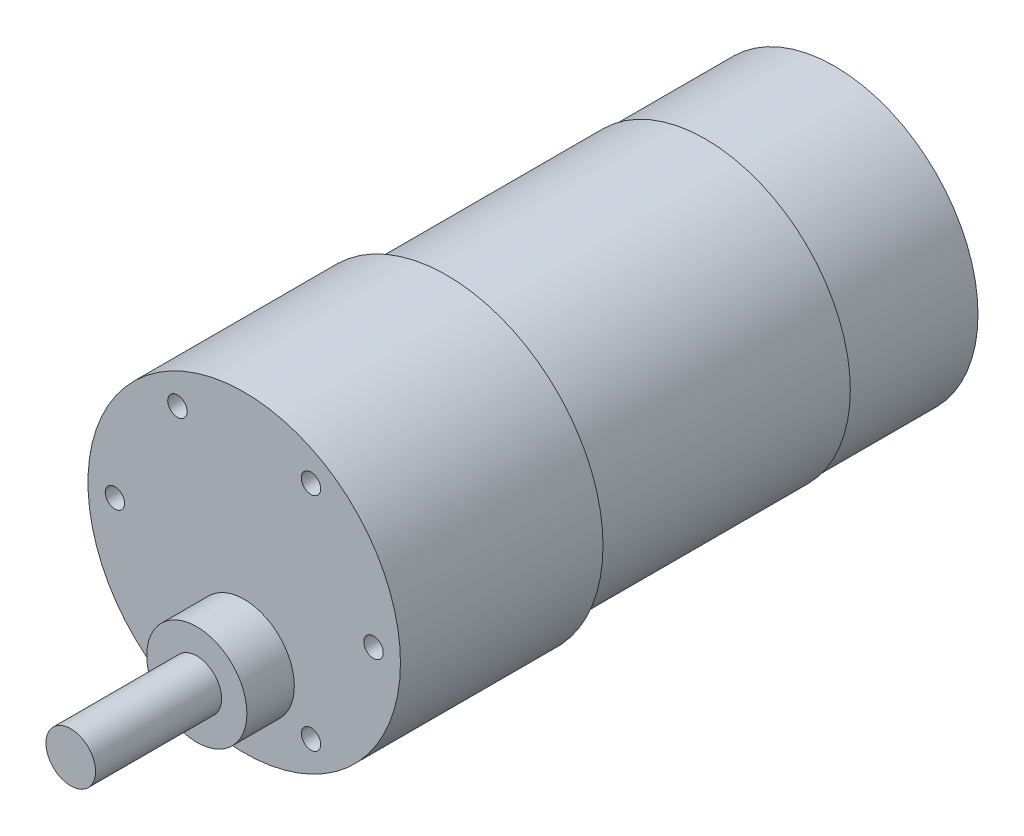
SolidWorks part; units mm, degrees
ref_plane "Front Plane" through (0, 0, 0) normal (0, 0, 1) x (1, 0, 0)
ref_plane "Top Plane" through (0, 0, 0) normal (0, 1, 0) x (1, 0, 0)
ref_plane "Right Plane" through (0, 0, 0) normal (1, 0, 0) x (0, 0, -1)
sketch "Sketch1" plane through (0, 0, 0) normal (0, 0, 1) x (1, 0, 0)
  circle A0 centre (0, 0) radius 18.415
  dimension "D1" = 36.83
extrude "Boss-Extrude1" add sketch "Sketch1" against normal blind 23.876
sketch "Sketch2" plane through (0, 0, 0) normal (0, 0, 1) x (1, 0, 0)
  circle A0 centre (0, -8.636) radius 5.9055
  dimension "D1" = 11.811
  dimension "D2" = 8.636
extrude "Boss-Extrude2" add sketch "Sketch2" along normal blind 5.588
sketch "Sketch3" plane through (0, 0, 5.588) normal (0, 0, 1) x (1, 0, 0)
  circle A0 centre (0, -8.636) radius 2.921
  circle A1 centre (0, -8.636) radius 5.9055 construction
  dimension "D1" = 5.842
extrude "Boss-Extrude3" add sketch "Sketch3" along normal blind 14.859
sketch "Sketch4" plane through (0, 0, -23.876) normal (0, 0, -1) x (-1, 0, 0)
  circle A0 centre (0, 0) radius 17.0815
  dimension "D1" = 34.163
extrude "Boss-Extrude4" add sketch "Sketch4" along normal blind 30.48
sketch "Sketch5" plane through (0, 0, -54.356) normal (0, 0, -1) x (-1, 0, 0)
  circle A0 centre (0, 0) radius 16.891
  dimension "D1" = 33.782
extrude "Boss-Extrude5" add sketch "Sketch5" along normal blind 15.24
sketch "Sketch6" plane through (0, 0, 0) normal (0, 0, 1) x (1, 0, 0)
  circle A0 centre (7.8719, -13.0496) radius 1.143
  circle A1 centre (15.24, 0) radius 1.143
  circle A2 centre (7.8719, 13.0496) radius 1.143
  dimension "D1" = 2.286
  dimension "D2" = 2.286
  dimension "D3" = 2.286
  dimension "D4" = 15.24
  dimension "D5" = 15.24
  dimension "D6" = 15.24
  dimension "D7" = 14.986
extrude "Cut-Extrude1" cut sketch "Sketch6" against normal blind 15.24
pattern_circular "CirPattern1" count 2 over 360 about axis through (0, 0, 0) along (0, 0, 1) of "Cut-Extrude1"
ref_plane "Plane1" through (0, -16.891, 0) normal (0, -1, 0) x (-1, 0, 0)
sketch "Sketch8" plane through (0, -16.891, 0) normal (0, -1, 0) x (-1, 0, 0)
  line L0 (17.0815, 54.356) -> (-17.0815, 54.356) construction
  line L1 (-7.112, 60.579) -> (7.112, 60.579)
  line L2 (-7.112, 60.579) -> (-7.112, 56.896)
  line L3 (-7.112, 56.896) -> (7.112, 56.896)
  line L4 (7.112, 60.579) -> (7.112, 56.896)
  point P4 (0, 60.579)
  dimension "D1" = 14.224
  dimension "D2" = 14.224
  dimension "D3" = 3.683
  dimension "D4" = 2.54
extrude "Cut-Extrude2" cut sketch "Sketch8" against normal blind 2.54
